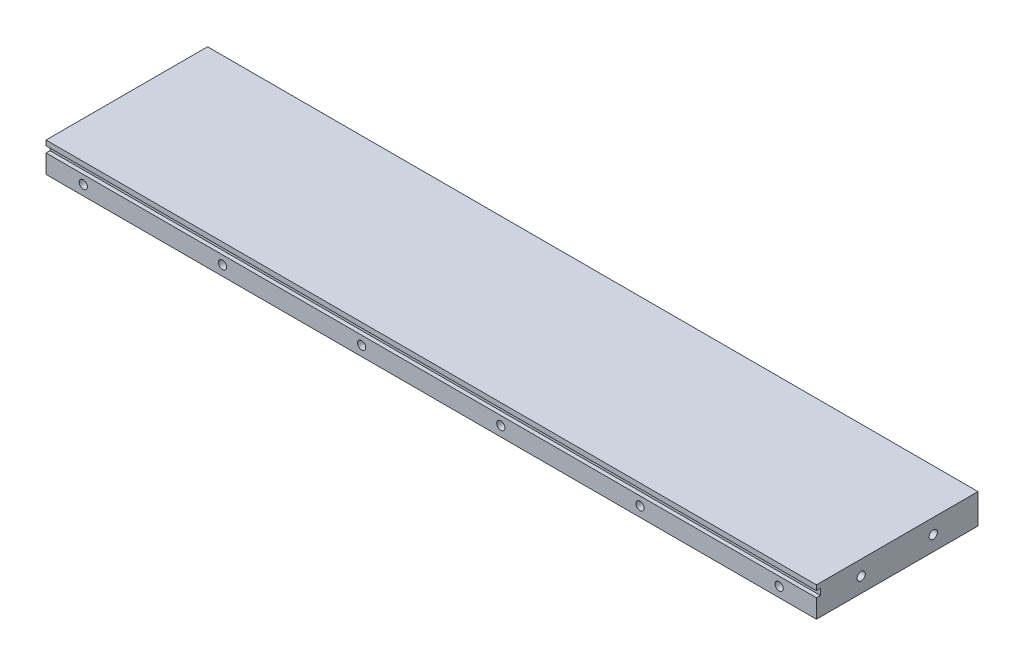
SolidWorks part; units mm, degrees
material "ABS PC"
ref_plane "Ebene vorne" through (0, 0, 0) normal (0, 0, 1) x (1, 0, 0)
ref_plane "Ebene oben" through (0, 0, 0) normal (0, 1, 0) x (1, 0, 0)
ref_plane "Ebene rechts" through (0, 0, 0) normal (1, 0, 0) x (0, 0, -1)
sketch "Skizze1" plane through (0, 0, 0) normal (0, 0, 1) x (1, 0, 0)
  line L1 (0, 0) -> (310, 0)
  line L2 (0, 0) -> (0, 12)
  line L3 (0, 12) -> (310, 12)
  line L4 (310, 0) -> (310, 12)
  dimension "D1" = 12
  dimension "D2" = 310
extrude "Aufsatz-Linear austragen1" add sketch "Skizze1" against normal blind 65
sketch "Skizze2" plane through (0, 0, 0) normal (0, 0, 1) x (1, 0, 0)
  line L7 (310, 0) -> (310, 12) construction
  line L8 (310, 10) -> (0, 10)
  line L9 (310, 10) -> (310, 7.5)
  line L10 (310, 7.5) -> (0, 7.5)
  line L11 (0, 10) -> (0, 7.5)
  line L12 (0, 12) -> (0, 0) construction
  line L13 (310, 12) -> (0, 12) construction
  dimension "D1" = 2.5
  dimension "D2" = 2
extrude "Schnitt-Linear austragen1" cut sketch "Skizze2" against normal blind 1.6
hole_wizard "M4 Gewindebohrung1" positions "3D-Skizze1" profile "Skizze3" tap size "M4" standard "DIN"
sketch3d "3D-Skizze1"
  line L0 (0, 4, 0) -> (310, 4, 0) construction
  line L1 (0, 7.5, 0) -> (0, 0, 0) construction
  line L2 (310, 0, 0) -> (310, 7.5, 0) construction
  line L4 (0, 0, 0) -> (310, 0, 0) construction
  point P10 (15, 4, 0)
  point P12 (71, 4, 0)
  point P14 (127, 4, 0)
  point P16 (183, 4, 0)
  point P20 (239, 4, 0)
  point P22 (295, 4, 0)
  point P28 (15, 4, 0)
  point P30 (71, 4, 0)
  point P32 (15, 4, 0)
  point P34 (15, 4, 0)
  point P36 (71, 4, 0)
  point P38 (127, 4, 0)
  point P40 (183, 4, 0)
  point P42 (239, 4, 0)
  point P44 (295, 4, 0)
  point P49 (295, 4, 0)
  point P56 (295, 4, 0)
  point P71 (15, 1.7227, 0)
  dimension "D1" = 4
  dimension "D2" = 15
  dimension "D3" = 15
  dimension "D4" = 56
  dimension "D5" = 56
  dimension "D6" = 56
  dimension "D7" = 56
sketch "Skizze3" plane through (295, 4, 0) normal (1, 0, 0) x (0, -1, 0)
  line L0 (0, 0) -> (0, 12.4914)
  line L1 (0, 12.4914) -> (1.65, 11.5)
  line L2 (1.65, 11.5) -> (1.65, 0)
  line L5 (1.65, 0) -> (0, 0)
  line L10 (0, 12.4914) -> (-1.65, 11.5) construction
  line L11 (0, -6.35) -> (0, 107.95) construction
  dimension "Bohrerdurchmesser" = 3.3
  dimension "Bohrungstiefe" = 11.5
  dimension "Spitzenwinkel" = 118
cosmetic thread "Bohrungsgewinde43"
cosmetic thread "Bohrungsgewinde44"
cosmetic thread "Bohrungsgewinde45"
cosmetic thread "Bohrungsgewinde46"
cosmetic thread "Bohrungsgewinde47"
cosmetic thread "Bohrungsgewinde48"
ref_plane "Ebene1" through (155, 0, 0) normal (1, 0, 0) x (0, 0, -1)
hole_wizard "M4 Gewindebohrung2" positions "3D-Skizze2" profile "Skizze4" tap size "M4" standard "DIN"
sketch3d "3D-Skizze2"
  line L0 (0, 6, -65) -> (0, 6, 2.4822) construction
  line L1 (0, 12, -65) -> (0, 0, -65) construction
  point P2 (0, 6, -18)
  point P4 (0, 6, -47)
  point P19 (0, 0, 0)
  dimension "D1" = 18
  dimension "D3" = 47
sketch "Skizze4" plane through (0, 6, -18) normal (0, 1, 0) x (0, 0, 1)
  line L0 (0, 0) -> (0, 12.4914)
  line L1 (0, 12.4914) -> (1.65, 11.5)
  line L2 (1.65, 11.5) -> (1.65, 0)
  line L5 (1.65, 0) -> (0, 0)
  line L10 (0, 12.4914) -> (-1.65, 11.5) construction
  line L11 (0, -6.35) -> (0, 107.95) construction
  dimension "Bohrerdurchmesser" = 3.3
  dimension "Bohrungstiefe" = 11.5
  dimension "Spitzenwinkel" = 118
cosmetic thread "Bohrungsgewinde35"
cosmetic thread "Bohrungsgewinde36"
mirror "Spiegeln2" about plane through (155, 0, 0) normal (1, 0, 0) of "M4 Gewindebohrung2"
cosmetic thread "Bohrungsgewinde49"
cosmetic thread "Bohrungsgewinde50"
